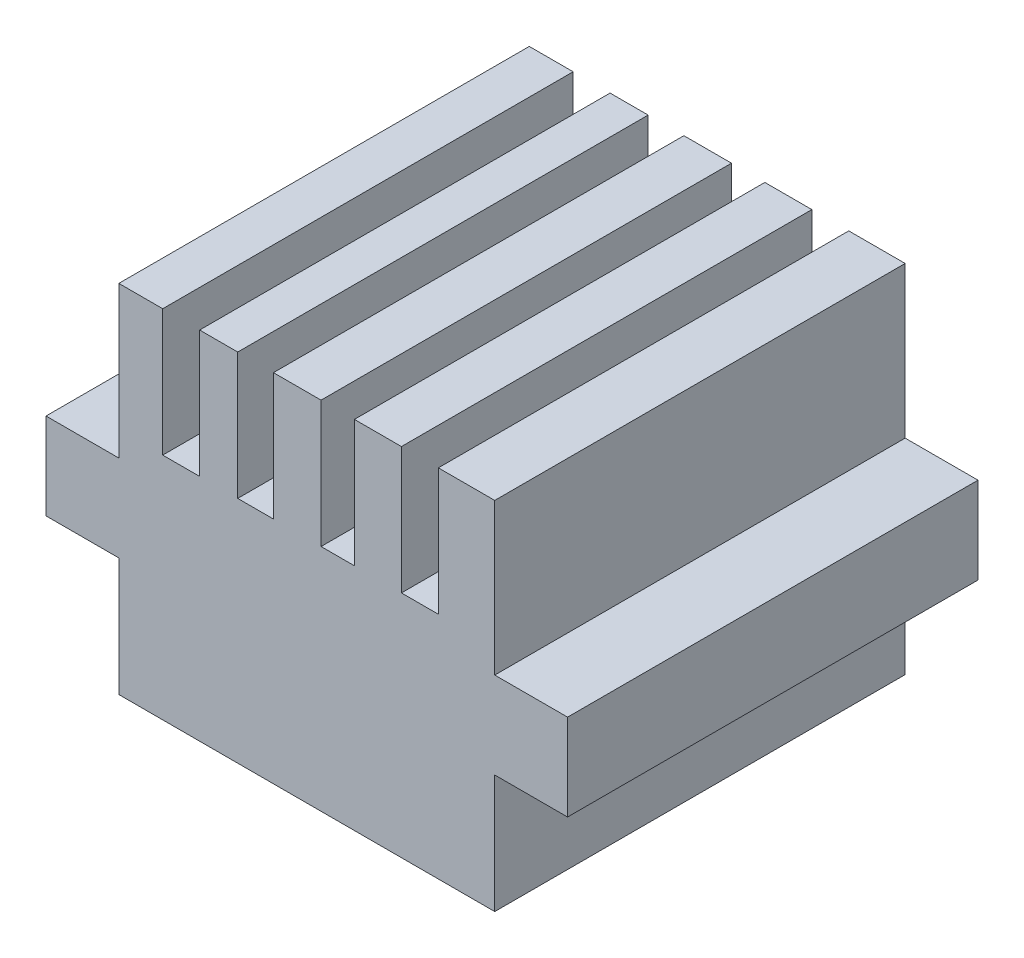
SolidWorks part; units mm, degrees
ref_plane "Alzado" through (0, 0, 0) normal (0, 0, 1) x (1, 0, 0)
ref_plane "Planta" through (0, 0, 0) normal (0, 1, 0) x (1, 0, 0)
ref_plane "Vista lateral" through (0, 0, 0) normal (1, 0, 0) x (0, 0, -1)
sketch "Croquis1" plane through (0, 0, 0) normal (0, 1, 0) x (1, 0, 0)
  line L1 (0, 0) -> (28.85, 0)
  line L2 (0, 0) -> (0, 31.5)
  line L3 (0, 31.5) -> (28.85, 31.5)
  line L4 (28.85, 0) -> (28.85, 31.5)
  dimension "D1" = 31.5
  dimension "D2" = 28.85
extrude "Saliente-Extruir1" add sketch "Croquis1" along normal blind 17.6
sketch "Croquis3" plane through (0, 17.6, 0) normal (0, 1, 0) x (1, 0, 0)
  line L0 (0, 0) -> (28.85, 0) construction
  line L1 (0, 31.5) -> (3.3685, 31.5)
  line L2 (0, 31.5) -> (0, 0)
  line L3 (0, 0) -> (3.3685, 0)
  line L4 (3.3685, 31.5) -> (3.3685, 0)
  line L5 (28.85, 31.5) -> (0, 31.5) construction
  line L6 (28.85, 31.5) -> (24.5221, 31.5)
  line L7 (28.85, 31.5) -> (28.85, 0)
  line L8 (28.85, 0) -> (24.5221, 0)
  line L9 (24.5221, 31.5) -> (24.5221, 0)
  line L10 (21.6894, 31.5) -> (18.0801, 31.5)
  line L11 (21.6894, 31.5) -> (21.6894, 0)
  line L12 (21.6894, 0) -> (18.0801, 0)
  line L13 (18.0801, 31.5) -> (18.0801, 0)
  line L15 (15.5215, 31.5) -> (11.8665, 31.5)
  line L16 (15.5215, 31.5) -> (15.5215, 0)
  line L17 (15.5215, 0) -> (11.8665, 0)
  line L18 (11.8665, 31.5) -> (11.8665, 0)
  line L19 (9.1252, 31.5) -> (6.2011, 31.5)
  line L20 (9.1252, 31.5) -> (9.1252, 0)
  line L21 (9.1252, 0) -> (6.2011, 0)
  line L22 (6.2011, 31.5) -> (6.2011, 0)
extrude "Saliente-Extruir2" add sketch "Croquis3" along normal blind 9.73
sketch "Croquis4" plane through (0, 0, 0) normal (-1, 0, 0) x (0, 0, 1)
  line L0 (-31.5, 27.33) -> (-31.5, 0) construction
  line L1 (-31.5, 9.08) -> (0, 9.08)
  line L2 (-31.5, 9.08) -> (-31.5, 15.72)
  line L3 (-31.5, 15.72) -> (0, 15.72)
  line L4 (0, 9.08) -> (0, 15.72)
  line L5 (0, 27.33) -> (0, 0) construction
  line L6 (-31.5, 0) -> (0, 0) construction
  dimension "D1" = 9.08
  dimension "D2" = 6.64
extrude "Saliente-Extruir3" add sketch "Croquis4" along normal blind 5.59
sketch "Croquis5" plane through (28.85, 0, 0) normal (1, 0, 0) x (0, 0, -1)
  line L0 (0, 27.33) -> (0, 0) construction
  line L1 (0, 15.72) -> (31.5, 15.72)
  line L2 (0, 15.72) -> (0, 9.08)
  line L3 (0, 9.08) -> (31.5, 9.08)
  line L4 (31.5, 15.72) -> (31.5, 9.08)
  line L5 (31.5, 27.33) -> (31.5, 0) construction
  line L6 (0, 0) -> (31.5, 0) construction
  dimension "D1" = 6.64
  dimension "D2" = 9.08
extrude "Saliente-Extruir4" add sketch "Croquis5" along normal blind 5.59
